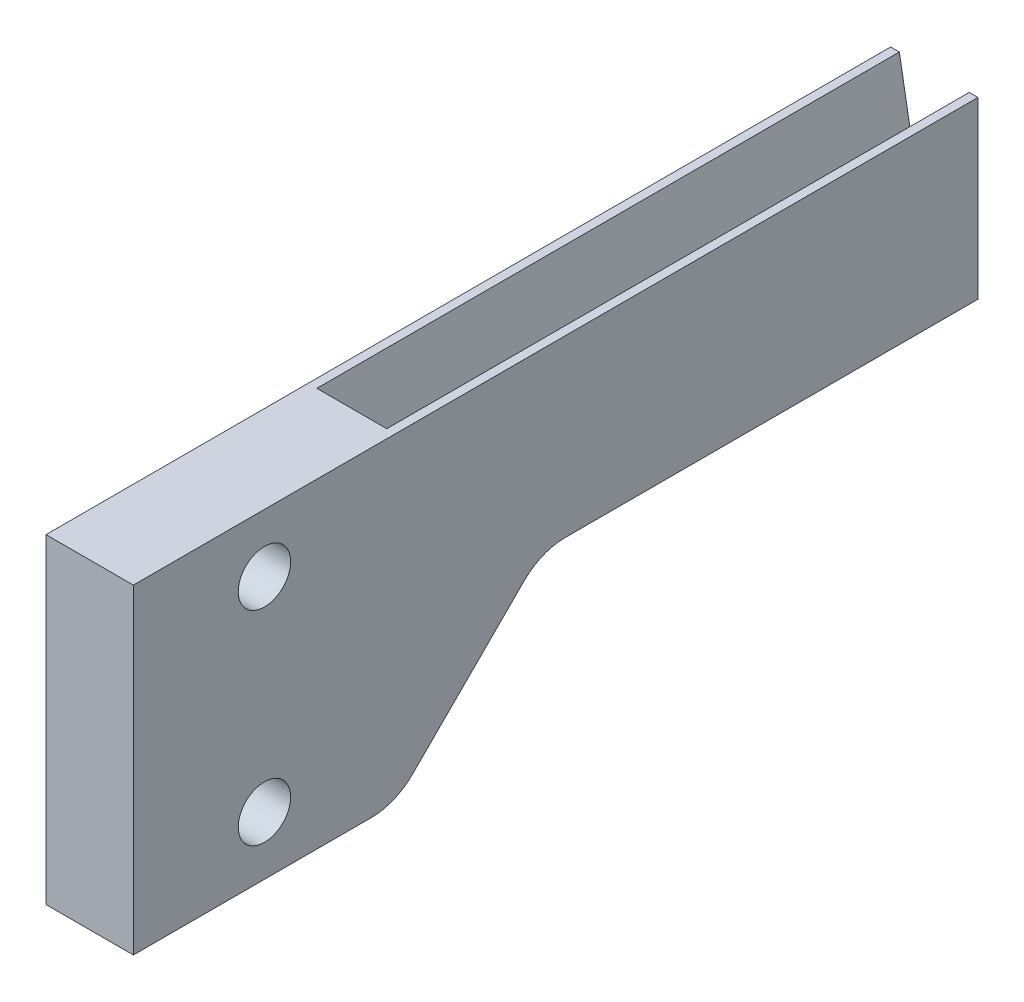
SolidWorks part; units mm, degrees
ref_plane "Ebene vorne" through (0, 0, 0) normal (0, 0, 1) x (1, 0, 0)
ref_plane "Ebene oben" through (0, 0, 0) normal (0, 1, 0) x (1, 0, 0)
ref_plane "Ebene rechts" through (0, 0, 0) normal (1, 0, 0) x (0, 0, -1)
sketch "Skizze1" plane through (0, 0, 0) normal (0, 0, 1) x (1, 0, 0)
  line L0 (-5.5, 0) -> (-5.5, 30)
  line L1 (55, 0) -> (-55, 0) construction
  line L2 (-5.5, 30) -> (-4, 30)
  line L3 (-4, 30) -> (0, 7.3149)
  line L4 (0, -55) -> (0, 55) construction
  line L5 (0, 7.3149) -> (4, 7.3149)
  line L6 (4, 7.3149) -> (8, 30)
  line L7 (8, 30) -> (9.5, 30)
  line L8 (9.5, 30) -> (9.5, 0)
  line L9 (9.5, 0) -> (-5.5, 0)
  dimension "D1" = 4
  dimension "D2" = 100
  dimension "D3" = 100
  dimension "D4" = 12
  dimension "D5" = 30
  dimension "D6" = 15
extrude "Aufsatz-Linear austragen1" add sketch "Skizze1" along normal blind 100
sketch "Skizze4" plane through (-5.5, 0, 0) normal (-1, 0, 0) x (0, 0, 1)
  line L0 (122.5, 30) -> (122.5, -50) construction
  line L1 (100, 30) -> (145, 30)
  line L2 (100, 30) -> (100, 0)
  line L4 (145, 30) -> (145, -25)
  line L5 (97.0711, -22.0711) -> (75, 0)
  line L6 (75, 0) -> (100, 0)
  line L7 (8.25, 0) -> (-8.25, 0) construction
  line L9 (104.1421, -25) -> (145, -25)
  circle A0 centre (122.5, 20) radius 4.5
  circle A1 centre (122.5, -15) radius 4.5
  arc A3 (104.1421, -25) -> (97.0711, -22.0711) centre (104.1421, -15) cw
  point P11 (99.8505, -24.8505)
  point P12 (100, -25)
  point P20 (100, -25)
  dimension "D3" = 9
  dimension "D8" = 10
  dimension "D1" = 45
  dimension "D2" = 55
  dimension "D4" = 35
  dimension "D5" = 10
  dimension "D6" = 0
  dimension "D7" = 25
  dimension "D9" = 45
extrude "Aufsatz-Linear austragen2" add sketch "Skizze4" against normal blind 15
fillet "Verrundung1" radius 10 1 edges at (2, 0, 75)
